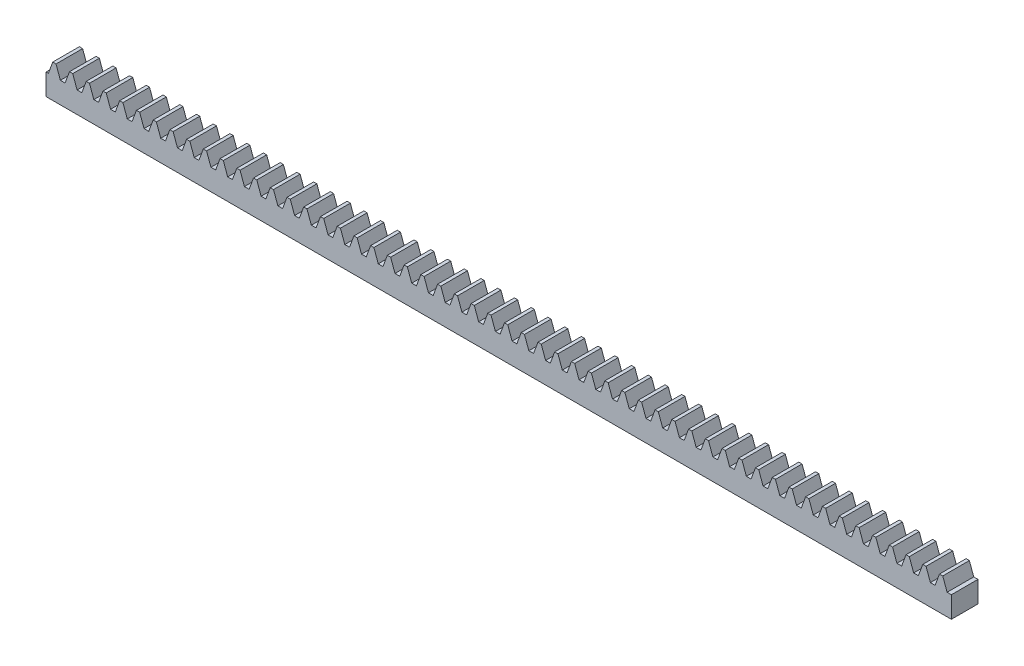
SolidWorks part; units mm, degrees
extrude "Blank" add sketch "BlankSke" against normal blind 6
sketch "BlankSke" plane through (0, 0, 0) normal (0, 0, 1) x (1, 0, 0)
  line L1 (0, 0) -> (170, 0)
  line L2 (0, 0) -> (0, 6.25)
  line L3 (0, 6.25) -> (170, 6.25)
  line L4 (170, 0) -> (170, 6.25)
  dimension "Length" = 170
  dimension "Blank_height" = 6.25
ref_plane "Plane1" through (0, 0, 0) normal (0, 0, 1) x (1, 0, 0)
ref_plane "Plane2" through (0, 0, 0) normal (0, 1, 0) x (1, 0, 0)
ref_plane "Plane3" through (0, 0, 0) normal (1, 0, 0) x (0, 0, -1)
other "Configuration Table"
sketch "HoldingSke" plane through (0, 0, 0) normal (0, 1, 0) x (1, 0, 0)
  line L0 (0, 0) -> (0.1392, 0.9903)
  line L1 (-15, 0) -> (100, 0) construction
  line L2 (0, 0) -> (-2.1039, 2.3779)
  line L3 (0, 0) -> (-11.863, 4.5341)
  line L4 (0, 0) -> (4.8292, 7.1596)
  line L5 (0, 0) -> (-23.7986, -8.8762)
  line L6 (0, 0) -> (-10.5278, -7.1032)
  line L9 (-71.009, 38.7566) -> (88.7388, 96.9)
  line L10 (-76.2, 3.3779) -> (-70.95, 3.3779)
  line L11 (0, 0) -> (-6, 0)
  line L12 (-76.2, 101.6) -> (-76.162, 101.6)
  line L13 (24.9733, 27.94) -> (52.9518, 28.4284)
  line L14 (24.9733, 27.94) -> (24.9743, 27.94)
  line L15 (24.9733, 27.94) -> (100.4006, 29.5858)
  circle A0 centre (0, 0) radius 19.05
  circle A1 centre (0, 0) radius 2.625
  circle A2 centre (0, 0) radius 12.7
  dimension "MPH" = 5.25
  dimension "Diameter" = 38.1
  dimension "Num_teeth" = 56
  dimension "Pitch" = 1
  dimension "Show_teeth" = 998
  dimension "Thickness" = 12.7
  dimension "Ap" = 20
  dimension "Pitch_height" = 5.25
  dimension "Width" = 6
  dimension "Backlash" = 0.038
  dimension "Addendum_fac" = 1
  dimension "Dedendum_fac" = 1.25
  dimension "Clearance_fac" = 0.25
  dimension "Dedendum_add" = 0.001
  dimension "Length" = 170
  dimension "Module" = 1
sketch "TooCutSkeIll" plane through (0, 0, 0) normal (0, 0, 1) x (1, 0, 0)
  line L0 (-1.2538, 6.2237) -> (-0.5045, 4.1652)
  line L1 (-0.2687, 4) -> (0.2687, 4)
  line L2 (0.5045, 4.1652) -> (1.2538, 6.2237)
  line L3 (170, 6.25) -> (0, 6.25) construction
  line L4 (0, 0) -> (0, 64.897) construction
  line L5 (-13.208, 5.25) -> (12.954, 5.25) construction
  line L6 (0, 0) -> (170, 0) construction
  line L7 (0.8994, 5.25) -> (0.8994, 48.7463) construction
  line L8 (-0.8994, 5.25) -> (-0.8994, 48.7463) construction
  line L9 (1.2914, 6.25) -> (1.2914, 6.2754)
  line L10 (-1.2914, 6.25) -> (-1.2914, 6.2754)
  line L11 (-1.2914, 6.2754) -> (1.2914, 6.2754)
  arc A0 (0.2687, 4) -> (0.5045, 4.1652) centre (0.2687, 4.251) ccw
  arc A1 (-0.5045, 4.1652) -> (-0.2687, 4) centre (-0.2687, 4.251) ccw
  arc A2 (1.2914, 6.25) -> (1.2538, 6.2237) centre (1.2914, 6.21) ccw
  arc A3 (-1.2538, 6.2237) -> (-1.2914, 6.25) centre (-1.2914, 6.21) ccw
  dimension "Pitch_height" = 5.25
  dimension "Addendum_plus" = 1.0254
  dimension "Pressure_angle" = 20
  dimension "Gap_width" = 1.7988
  dimension "Dedendum" = 1.25
extrude "ToothCutIll" [suppressed] cut sketch "TooCutSkeIll" against normal through all
sketch "TooCutSkeSim" plane through (0, 0, 0) normal (0, 0, 1) x (1, 0, 0)
  line L0 (0.4444, 4) -> (-0.4444, 4)
  line L1 (1.2726, 6.2754) -> (0.4444, 4)
  line L2 (0, 17.4625) -> (0, 53.467) construction
  line L3 (1.2726, 6.2754) -> (-1.2726, 6.2754)
  line L6 (-1.2726, 6.2754) -> (-0.4444, 4)
  line L9 (-0.8994, 5.25) -> (0.8994, 5.25) construction
  line L10 (0, 0) -> (170, 0) construction
  line L11 (0.8994, 5.25) -> (0.8994, 53.467) construction
  line L12 (-0.8994, 5.25) -> (-0.8994, 53.467) construction
  dimension "Pitch_height" = 5.25
  dimension "Addendum_plus" = 1.0254
  dimension "Pressure_angle" = 20
  dimension "Gap_width" = 1.7988
  dimension "Dedendum" = 1.25
extrude "ToothCutSim" cut sketch "TooCutSkeSim" against normal through all
pattern_linear "TeethCuts" count 55 spacing 3.1416 along (1, 0, 0) of "ToothCutIll", "ToothCutSim"
sketch "Sketch1" plane through (170, 0, 0) normal (1, 0, 0) x (0, 0, -1)
  line L0 (6, 6.25) -> (0, 6.25) construction
  line L1 (0, 0) -> (1, 0)
  line L2 (0, 0) -> (0, 6.25)
  line L3 (0, 6.25) -> (1, 6.25)
  line L4 (1, 0) -> (1, 6.25)
  dimension "D1" = 1
extrude "Cut-Extrude1" cut sketch "Sketch1" against normal through all
equation "' \"Module@HoldingSke\" = 6.35"
equation "' \"Num_teeth@HoldingSke\" = 12"
equation "' \"Ap@HoldingSke\" =  20"
equation "' \"Ap@HoldingSke\" = 20"
equation "' \"Width@HoldingSke\" = 0.25 * 25.4"
equation "' \"Show_teeth@HoldingSke\" = 500"
equation "' \"Backlash@HoldingSke\" = 0.009 * 25.4"
equation "' \"Addendum_fac@HoldingSke\" = 1.0"
equation "' \"Dedendum_fac@HoldingSke\" = 1.25"
equation "' \"Dedendum_add@HoldingSke\" = 0.00005 * 25.4"
equation "' \"Clearance_fac@HoldingSke\" = 0.25"
equation "' \"Pitch_height@HoldingSke\" = 1 * 25.4"
equation "' \"Length@HoldingSke\" = 4.71 * 25.4"
equation "\"Pitch@HoldingSke\" = 1 / \"Module@HoldingSke\""
equation "\"MPH@HoldingSke\" = \"Dedendum_fac@HoldingSke\" / \"Pitch@HoldingSke\" + 2 * \"Dedendum_add@HoldingSke\" + 0.002 * 25.4"
equation "\"MPH@HoldingSke\" = ((sgn( \"MPH@HoldingSke\" - \"Pitch_height@HoldingSke\")+1)*( \"MPH@HoldingSke\" - \"Pitch_height@HoldingSke\"))/2 + \"Pitch_height@HoldingSke\""
equation "\"Blank_height@BlankSke\" = \"Pitch_height@HoldingSke\" + \"Addendum_fac@HoldingSke\"  / \"Pitch@HoldingSke\" "
equation "\"Length@BlankSke\" =  \"Length@HoldingSke\""
equation "\"Face_width@Blank\" = \"Width@HoldingSke\""
equation "\"Pressure_angle@TooCutSkeIll\" = \"Ap@HoldingSke\""
equation "\"Addendum_plus@TooCutSkeIll\" =  \"Addendum_fac@HoldingSke\"  / \"Pitch@HoldingSke\" + 0.001 *25.4"
equation "\"Dedendum@TooCutSkeIll\" = \"Dedendum_fac@HoldingSke\"  / \"Pitch@HoldingSke\""
equation "\"Pitch_height@TooCutSkeIll\" =  \"MPH@HoldingSke\""
equation "\"Gap_width@TooCutSkeIll\" = 3.14159265 / 2 / \"Pitch@HoldingSke\" + 6 * \"Backlash@HoldingSke\""
equation "\"Pressure_angle@TooCutSkeSim\" = \"Ap@HoldingSke\""
equation "\"Addendum_plus@TooCutSkeSim\" =  \"Addendum_fac@HoldingSke\"  / \"Pitch@HoldingSke\" + 0.001 * 25.4"
equation "\"Dedendum@TooCutSkeSim\" = \"Dedendum_fac@HoldingSke\"  / \"Pitch@HoldingSke\""
equation "\"Pitch_height@TooCutSkeSim\" =  \"MPH@HoldingSke\""
equation "\"Gap_width@TooCutSkeSim\" = 3.14159265 / 2 / \"Pitch@HoldingSke\" + 6 * \"Backlash@HoldingSke\""
equation "\"Root_fillet@TooCutSkeIll\" = \"Clearance_fac@HoldingSke\" / \"Pitch@HoldingSke\" + \"Dedendum_add@HoldingSke\""
equation "\"Break_rad@TooCutSkeIll\" = 0.02 / \"Pitch@HoldingSke\" * 2"
equation "\"Linear_pitch@TeethCuts\" = 3.14159265 / \"Pitch@HoldingSke\""
equation "\"Num_teeth@HoldingSke\" = int( ( \"Length@HoldingSke\" + 0 ) / (3.14159265 / \"Pitch@HoldingSke\")) + 0.9999  + 1"
equation " \"Num_teeth@TeethCuts\" = int( \"Show_teeth@HoldingSke\" ) + 1"
equation " \"Num_teeth@TeethCuts\" = ((sgn( \"Num_teeth@TeethCuts\" - \"Num_teeth@HoldingSke\" )-1)*( \"Num_teeth@TeethCuts\" - \"Num_teeth@HoldingSke\" ))/-2+ \"Num_teeth@HoldingSke\""
equation " \"Num_teeth@TeethCuts\" = ((sgn( \"Num_teeth@TeethCuts\" - 2.0)+1)*( \"Num_teeth@TeethCuts\" - 2.0))/2 +2.0"
